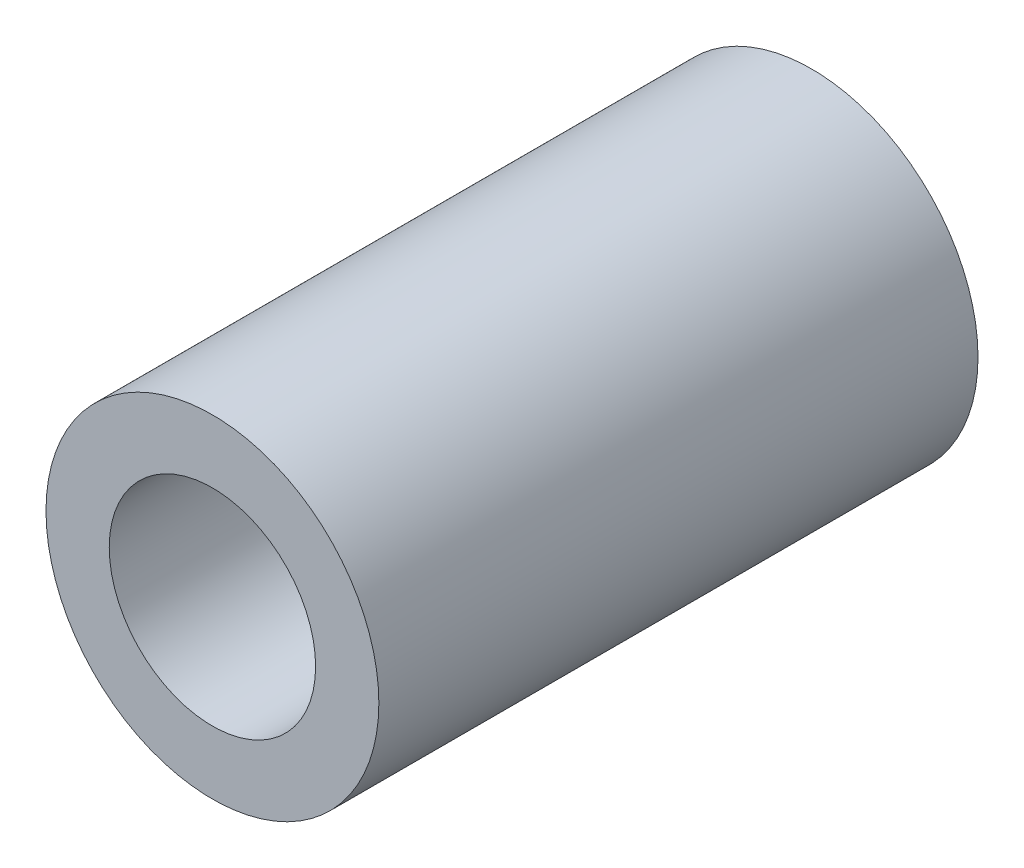
SolidWorks part; units mm, degrees
ref_plane "Front Plane" through (0, 0, 0) normal (0, 0, 1) x (1, 0, 0)
ref_plane "Top Plane" through (0, 0, 0) normal (0, 1, 0) x (1, 0, 0)
ref_plane "Right Plane" through (0, 0, 0) normal (1, 0, 0) x (0, 0, -1)
sketch "Sketch1" plane through (0, 0, 0) normal (0, 0, 1) x (1, 0, 0)
  circle A0 centre (0, 0) radius 2.5
  circle A1 centre (0, 0) radius 1.55
  dimension "D1" = 5
  dimension "D2" = 3.1
extrude "Boss-Extrude1" add sketch "Sketch1" along normal blind 9
